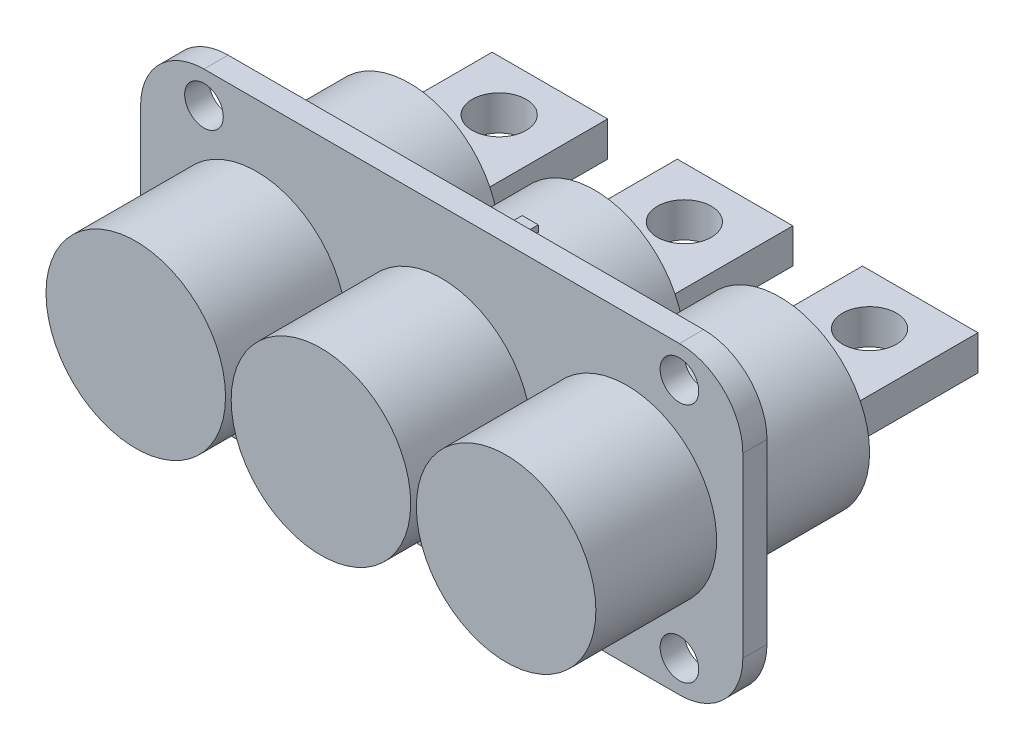
SolidWorks part; units mm, degrees
ref_plane "Front Plane" through (0, 0, 0) normal (0, 0, 1) x (1, 0, 0)
ref_plane "Top Plane" through (0, 0, 0) normal (0, 1, 0) x (1, 0, 0)
ref_plane "Right Plane" through (0, 0, 0) normal (1, 0, 0) x (0, 0, -1)
sketch "Sketch1" plane through (0, 0, 0) normal (0, 0, 1) x (1, 0, 0)
  circle A0 centre (0, 0) radius 14.1605
  dimension "D1" = 28.321
extrude "Boss-Extrude1" add sketch "Sketch1" along normal blind 43.18
sketch "Sketch3" plane through (0, 0, 0) normal (0, 1, 0) x (1, 0, 0)
  line L1 (-9.1123, 0) -> (9.1123, 0)
  line L2 (-9.1123, 0) -> (-9.1123, 22.1488)
  line L3 (-9.1123, 22.1488) -> (9.1122, 22.1488)
  line L4 (9.1123, 0) -> (9.1122, 22.1488)
  circle A0 centre (0, 14.1478) radius 4.2545
  point P4 (0, 0)
  dimension "D3" = 8.509
  dimension "D4" = 3.7465
  dimension "D1" = 18.2245
  dimension "D2" = 22.1488
extrude "Boss-Extrude2" add sketch "Sketch3" along normal blind 2.7495 and the other way blind 2.7495
pattern_linear "LPattern1" count 2 spacing 29.21 along (1, 0, 0) count 2 spacing 29.21 along (-1, 0, 0) of bodies 102
sketch "Sketch4" plane through (0, 0, 0) normal (0, 0, 1) x (1, 0, 0)
  line L0 (-37.5, 24) -> (37.5, 24)
  line L1 (-37.5, -24) -> (37.5, -24)
  line L2 (-37.5, 19) -> (-37.5, -19) construction
  line L3 (0, 24) -> (0, -24) construction
  line L4 (47.5, 14) -> (47.5, -14)
  line L5 (-47.5, 14) -> (-47.5, -14)
  line L6 (-47.5, 0) -> (47.5, 0) construction
  line L7 (37.5, 19) -> (37.5, -19) construction
  arc A0 (-47.5, 14) -> (-37.5, 24) centre (-37.5, 14) cw
  arc A1 (37.5, 24) -> (47.5, 14) centre (37.5, 14) cw
  arc A2 (47.5, -14) -> (37.5, -24) centre (37.5, -14) cw
  arc A3 (-47.5, -14) -> (-37.5, -24) centre (-37.5, -14) ccw
  circle A4 centre (-37.5, 19) radius 3.048
  circle A5 centre (37.5, 19) radius 3.048
  circle A6 centre (37.5, -19) radius 3.048
  circle A7 centre (-37.5, -19) radius 3.048
  point P6 (0, 0)
  point P14 (0, 0)
  point P28 (37.5, 0)
  point P29 (-37.5, 0)
  dimension "D4" = 6.096
  dimension "D1" = 48
  dimension "D2" = 95
  dimension "D3" = 75
  dimension "D5" = 38
extrude "Boss-Extrude3" add sketch "Sketch4" along normal blind 3.81 from offset 20.32
sketch "Sketch6" plane through (0, 0, 43.18) normal (0, 0, 1) x (1, 0, 0)
  line L0 (-1.27, 14.1034) -> (-1.27, 15.1194)
  line L1 (-1.27, 15.1194) -> (1.27, 15.1194)
  line L2 (1.27, 15.1194) -> (1.27, 14.1034)
  line L3 (37.5, 24) -> (-37.5, 24) construction
  circle A0 centre (0, 0) radius 14.1605 construction
  circle A2 centre (0, 0) radius 14.1605
  arc A3 (1.27, 14.1034) -> (-1.27, 14.1034) centre (0, 0) ccw
  point P4 (0, 15.1194)
  point P7 (0, 24)
  dimension "D1" = 2.54
  dimension "D2" = 1.016
  dimension "D3" = 0
extrude "Boss-Extrude4" add sketch "Sketch6" against normal blind 2.54 from offset 30.48
